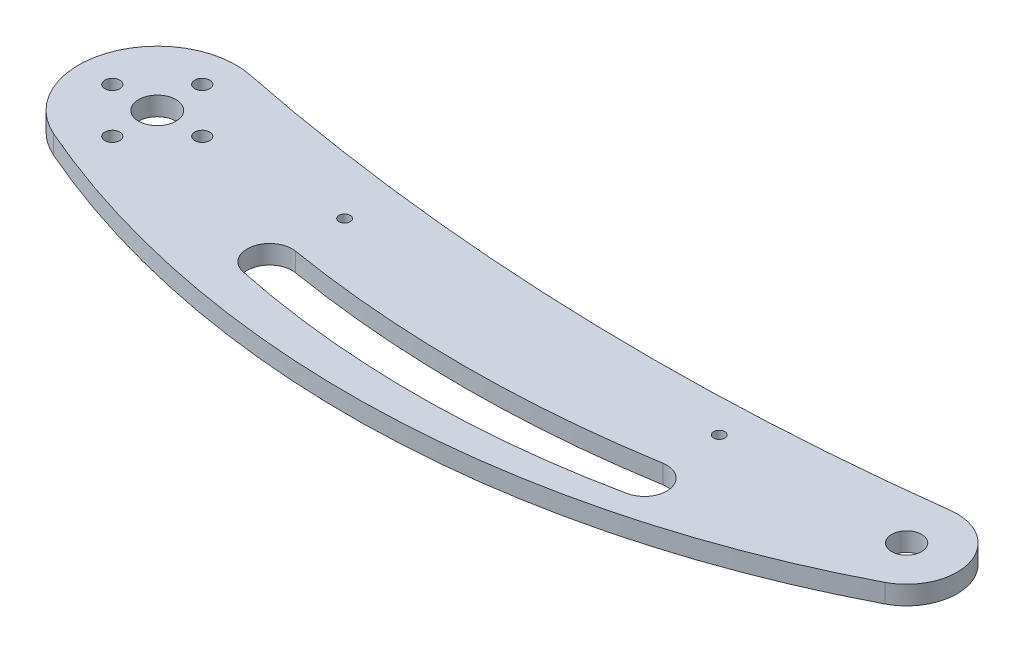
SolidWorks part; units mm, degrees
ref_plane "Front Plane" through (0, 0, 0) normal (0, 0, 1) x (1, 0, 0)
ref_plane "Top Plane" through (0, 0, 0) normal (0, 1, 0) x (1, 0, 0)
ref_plane "Right Plane" through (0, 0, 0) normal (1, 0, 0) x (0, 0, -1)
sketch "Sketch1" plane through (0, 0, 0) normal (0, 1, 0) x (1, 0, 0)
  line L0 (0, 0) -> (21, 0) construction
  line L1 (0, 0) -> (0, 21) construction
  line L2 (0, 0) -> (200, 0) construction
  circle A0 centre (0, 0) radius 5
  circle A1 centre (0, 0) radius 12 construction
  arc A2 (4.1644, 20.583) -> (-8.3699, -19.2599) centre (0, 0) ccw
  circle A3 centre (0, 12) radius 2
  circle A4 centre (0, 0) radius 12 construction
  circle A5 centre (12, 0) radius 2
  circle A6 centre (0, 0) radius 12 construction
  circle A7 centre (0, -12) radius 2
  circle A8 centre (0, 0) radius 12 construction
  circle A9 centre (-12, 0) radius 2
  circle A10 centre (200, 0) radius 4
  arc A11 (206.2065, -11.9887) -> (198.3089, 13.3937) centre (200, 0) ccw
  arc A12 (4.1644, 20.583) -> (198.3089, 13.3937) centre (123.1469, 608.6673) ccw
  arc A13 (-8.3699, -19.2599) -> (206.2065, -11.9887) centre (91.2719, 210.0249) ccw
  arc A14 (151.2295, -25.8727) -> (149.0196, -14.0806) centre (150, -20) ccw
  arc A15 (50.9804, -14.0806) -> (48.7705, -25.8727) centre (50, -20) ccw
  arc A17 (50.9804, -14.0806) -> (149.0196, -14.0806) centre (100, 281.8874) ccw
  circle A18 centre (50, 0) radius 1.5
  circle A19 centre (150, 0) radius 1.5
  arc A20 (48.7705, -25.8727) -> (151.2295, -25.8727) centre (100, 218.8221) ccw
  point P21 (0, 0)
  point P27 (48.7639, -25.8727)
  point P38 (154.5753, 0)
  point P39 (50, -19.2599)
  point P42 (150, -19.2599)
  point P43 (105.6563, 130.7642)
  point P44 (165.5882, 187.8257)
  dimension "D1" = 10
  dimension "D2" = 24
  dimension "D3" = 42
  dimension "D5" = 4
  dimension "D6" = 4
  dimension "D8" = 8
  dimension "D9" = 27
  dimension "D10" = 600
  dimension "D11" = 250
  dimension "D12" = 12
  dimension "D13" = 12
  dimension "D14" = 250
  dimension "D15" = 300
  dimension "D16" = 3
  dimension "D18" = 3
  dimension "D20" = 20
  dimension "D24" = 102.459
  dimension "D4" = 90
  dimension "D7" = 200
  dimension "D17" = 50
  dimension "D19" = 100
  dimension "D21" = 50
  dimension "D22" = 100
  dimension "D23" = 20
  dimension "D27" = 57.1404
extrude "Boss-Extrude1" add sketch "Sketch1" along normal blind 5
